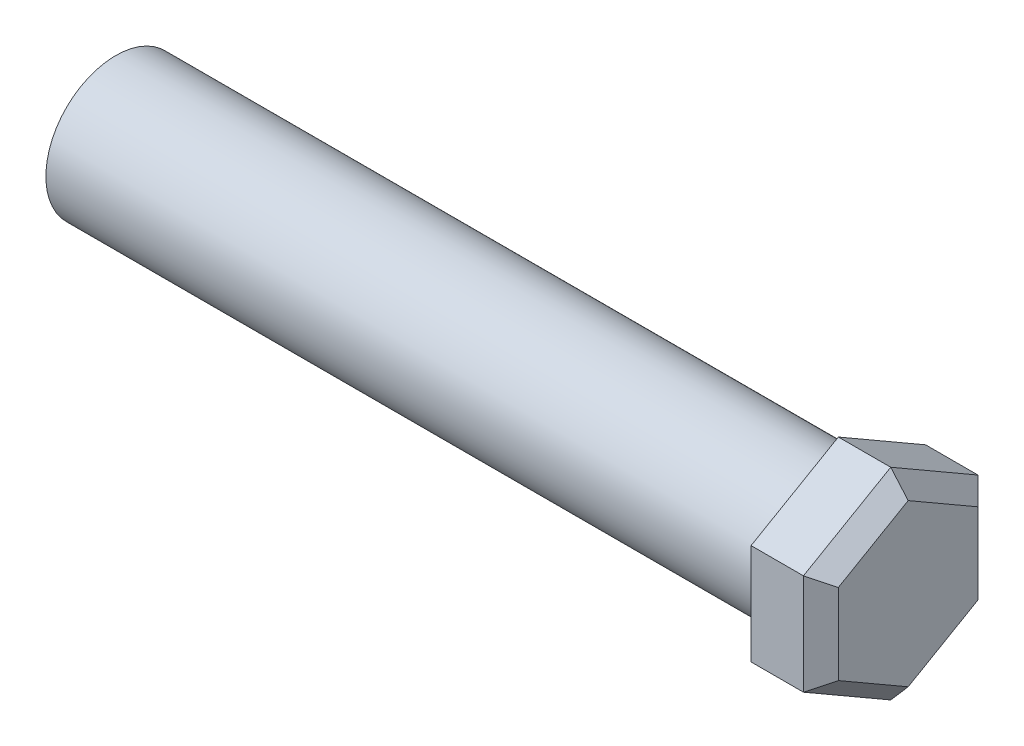
SolidWorks part; units mm, degrees
ref_plane "Front Plane" through (0, 0, 0) normal (0, 0, 1) x (1, 0, 0)
ref_plane "Top Plane" through (0, 0, 0) normal (0, 1, 0) x (1, 0, 0)
ref_plane "Right Plane" through (0, 0, 0) normal (1, 0, 0) x (0, 0, -1)
sketch "Sketch1" plane through (0, 0, 0) normal (1, 0, 0) x (0, 0, -1)
  circle A0 centre (0, 0) radius 2
  dimension "D1" = 4
extrude "Boss-Extrude1" add sketch "Sketch1" along normal blind 20.7
sketch "Sketch2" plane through (20.7, 0, 0) normal (1, 0, 0) x (0, 0, -1)
  line L1 (0, -2.8868) -> (2.5, -1.4434)
  line L2 (2.5, -1.4434) -> (2.5, 1.4434)
  line L3 (2.5, 1.4434) -> (0, 2.8868)
  line L4 (0, 2.8868) -> (-2.5, 1.4434)
  line L5 (-2.5, 1.4434) -> (-2.5, -1.4434)
  line L6 (-2.5, -1.4434) -> (0, -2.8868)
  circle A0 centre (0, 0) radius 2.5 construction
  dimension "D1" = 5.7735
extrude "Boss-Extrude2" add sketch "Sketch2" along normal blind 2
chamfer "Chamfer1" distance 0.5 angle 45 6 edges at (22.7, 0, 2.5) (22.7, 2.1651, 1.25) (22.7, 2.1651, -1.25) (22.7, 0, -2.5) (22.7, -2.1651, -1.25) (22.7, -2.1651, 1.25)
